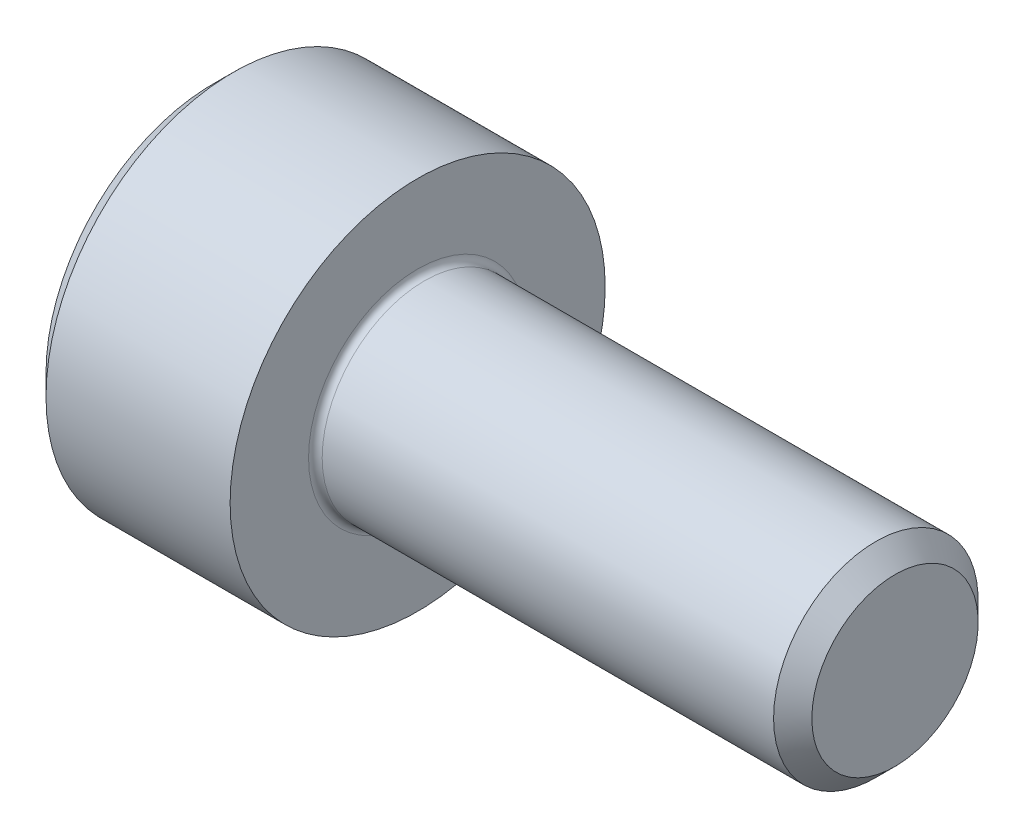
SolidWorks part; units mm, degrees
revolve "Base-Revolve" add sketch "BodySke"
sketch "BodySke" plane through (0, 0, 0) normal (0, 0, 1) x (1, 0, 0)
  line L0 (0, 0) -> (0, 2.45)
  line L1 (0.3, 2.75) -> (3, 2.75)
  line L2 (3, 2.75) -> (3, 1.5)
  line L3 (3, 1.5) -> (9.7195, 1.5)
  line L4 (10, 1.2195) -> (10, 0)
  line L5 (10, 0) -> (0, 0)
  line L6 (-31.75, 0) -> (127, 0) construction
  line L7 (0, 2.45) -> (0.3, 2.75)
  line L8 (10, 1.2195) -> (9.7195, 1.5)
  line L9 (0, -2.45) -> (0.3, -2.75) construction
  line L10 (10, -1.2195) -> (9.7195, -1.5) construction
  line L11 (3.5, 9.525) -> (3.5, 3.175) construction
  line L12 (3, 9.525) -> (3, 3.175) construction
  line L13 (-40, 9.525) -> (-40, 3.175) construction
  dimension "Diameter" = 3
  dimension "Head_ht" = 3
  dimension "Length" = 7
  dimension "Body_ch_ang" = 45
  dimension "Head_dia" = 5.5
  dimension "Head_ch_ang" = 45
  dimension "Minor_dia" = 2.439
  dimension "Advance" = 0.5
  dimension "Thread_nom" = 7
  dimension "Thread_length" = 50
  dimension "Head_ch_ht" = 0.3
cosmetic thread "ThreadCosmetic" [suppressed]
fillet "Fillet1" radius 0.1 1 edges at (3, 0, 1.5)
material "Plain Carbon Steel"
ref_plane "Plane1" through (0, 0, 0) normal (0, 0, 1) x (1, 0, 0)
ref_plane "Plane2" through (0, 0, 0) normal (0, 1, 0) x (1, 0, 0)
ref_plane "Plane3" through (0, 0, 0) normal (1, 0, 0) x (0, 0, -1)
sketch "Sketch2" plane through (0, 0, 0) normal (0, 0, 1) x (1, 0, 0)
  line L0 (0, 1.28) -> (1.3, 1.28)
  line L1 (1.3, 1.28) -> (2.039, 0)
  line L2 (-31.75, 0) -> (127, 0) construction
  line L3 (2.039, 0) -> (0, 0)
  line L4 (0, 0) -> (0, 1.28)
  line L5 (0, 2.45) -> (0, -2.45) construction
  line L6 (0, 0) -> (47.625, 0) construction
  line L7 (3, -2.75) -> (3, 2.75) construction
  dimension "D1" = 1.28
  dimension "D2" = 60
revolve "Hex-PreBroach" cut sketch "Sketch2" angle 360 about L6
sketch "Sketch3" plane through (0, 0, 0) normal (-1, 0, 0) x (0, 0.5, 0.866)
  line L0 (0.739, 1.28) -> (-0.739, 1.28)
  line L1 (-0.739, 1.28) -> (-1.478, 0)
  line L2 (0.739, 1.28) -> (1.478, 0)
  line L3 (0.739, -1.28) -> (1.478, 0)
  line L4 (0.739, -1.28) -> (-0.739, -1.28)
  line L5 (-0.739, -1.28) -> (-1.478, 0)
  dimension "D1" = 1.28
  dimension "D2" = 1.28
  dimension "Hex_size" = 2.56
extrude "Hex" cut sketch "Sketch3" against normal blind 1.3
sketch "Sketch4" plane through (0, 0, 0) normal (-1, 0, 0) x (0, 0, 1)
  line L0 (0, 0) -> (1.4605, 0)
  line L1 (0, 0) -> (6.1484, 3.5498) construction
  line L2 (0, 0) -> (0.7302, 1.2648)
  line L3 (1.2009, 0.3267) -> (1.3933, 0.4378)
  line L4 (0.8834, 0.8767) -> (1.0758, 0.9877)
  arc A0 (1.2009, 0.3267) -> (0.8834, 0.8767) centre (0, 0) ccw
  arc A1 (1.4605, 0) -> (1.3933, 0.4378) centre (0, 0) ccw
  arc A2 (0.7302, 1.2648) -> (1.0758, 0.9877) centre (0, 0) cw
  dimension "D1" = 30
  dimension "D2" = 60
  dimension "Spline_p_dim" = 0.635
  dimension "D3" = 0.3175
extrude "Spline" [suppressed] cut sketch "Sketch4" against normal blind 1.3
pattern_circular "CirPattern1" [suppressed] count 6 every 60
sketch "Sketch5" plane through (0, 0, 0) normal (0, 0, 1) x (1, 0, 0)
  line L0 (-31.75, 0) -> (127, 0) construction
  line L2 (0, 2.45) -> (0, -2.45) construction
  circle A0 centre (1.2, 0) radius 0.475
  dimension "Drilled_hole_dia" = 0.95
  dimension "Drilled_hole_loc" = 1.2
extrude "Hole" [suppressed] cut sketch "Sketch5" against normal through all and the other way through all
pattern_circular "Drilled-4" [suppressed] count 2 every 60
pattern_circular "Drilled-6" [suppressed] count 3 every 60
sketch "ThdSchSke" plane through (0, 0, 0) normal (0, 0, 1) x (1, 0, 0)
  line L0 (3.5, -1.2195) -> (3.3036, -1.5)
  line L1 (3.5, -1.2195) -> (3.6964, -1.5)
  line L2 (3.6964, -1.5) -> (3.6964, -1.875)
  line L3 (-3.175, 0) -> (5.1513, 0) construction
  line L5 (3.6964, -1.875) -> (3.3036, -1.875)
  line L6 (3.3036, -1.875) -> (3.3036, -1.5)
  line L7 (0, 2.45) -> (0, -2.45) construction
  dimension "Thread_minor" = 2.439
  dimension "Diameter" = 3
  dimension "Start" = 3.5
revolve "ThreadSchematic" [suppressed] cut sketch "ThdSchSke" angle 360 about L3
pattern_linear "ThdSchPat" [suppressed]
equation "\"D2@Sketch3\" = \"Hex_size@Sketch3\" / 2"
equation "\"D1@Sketch3\" = \"Hex_size@Sketch3\" / 2"
equation "\"D1@Sketch2\" = \"Hex_size@Sketch3\" / 2"
equation "\"D3@Sketch4\" = \"Spline_p_dim@Sketch4\" / 2"
equation "\"Thread_minor@ThreadCosmetic\"  =  \"Minor_dia@BodySke\""
equation "\"D2@CirPattern1\" = 360 / \"Num_teeth@CirPattern1\""
equation "\"Wall_thickness@Sketch2\" = \"Head_ht@BodySke\" - \"Key_eng@Hex\""
equation "\"Thread_length@ThreadCosmetic\" = ((sgn( (\"Length@BodySke\" - \"Advance@BodySke\" ) - \"Thread_nom@BodySke\" )-1)*( (\"Length@BodySke\" - \"Advance@BodySke\" ) - \"Thread_nom@BodySke\" ))/-2+ \"Thread_nom@BodySke\""
equation "\"Thread_minor@ThdSchSke\" = \"Minor_dia@BodySke\""
equation "\"Diameter@ThdSchSke\" = \"Diameter@BodySke\""
equation "\"Overcut@ThdSchSke\" = \"Diameter@BodySke\" * 1.25"
equation "\"Start@ThdSchSke\" = \"Head_ht@BodySke\" + \"Length@BodySke\" - \"Thread_length@ThreadCosmetic\"  '---Non-countersunk---"
equation "\"Num_threads@ThdSchPat\" = int( \"Thread_length@ThreadCosmetic\" / \"Advance@BodySke\" + 0.999 )  + 1"
equation "\"Advance@ThdSchPat\" = \"Thread_length@ThreadCosmetic\" /  (\"Num_threads@ThdSchPat\" - 1) 'relax it"
equation "\"Num_threads@ThdSchPat\" = \"Num_threads@ThdSchPat\" - sgn( \"Num_threads@ThdSchPat\" - 1) '---chamfered tips only---"
